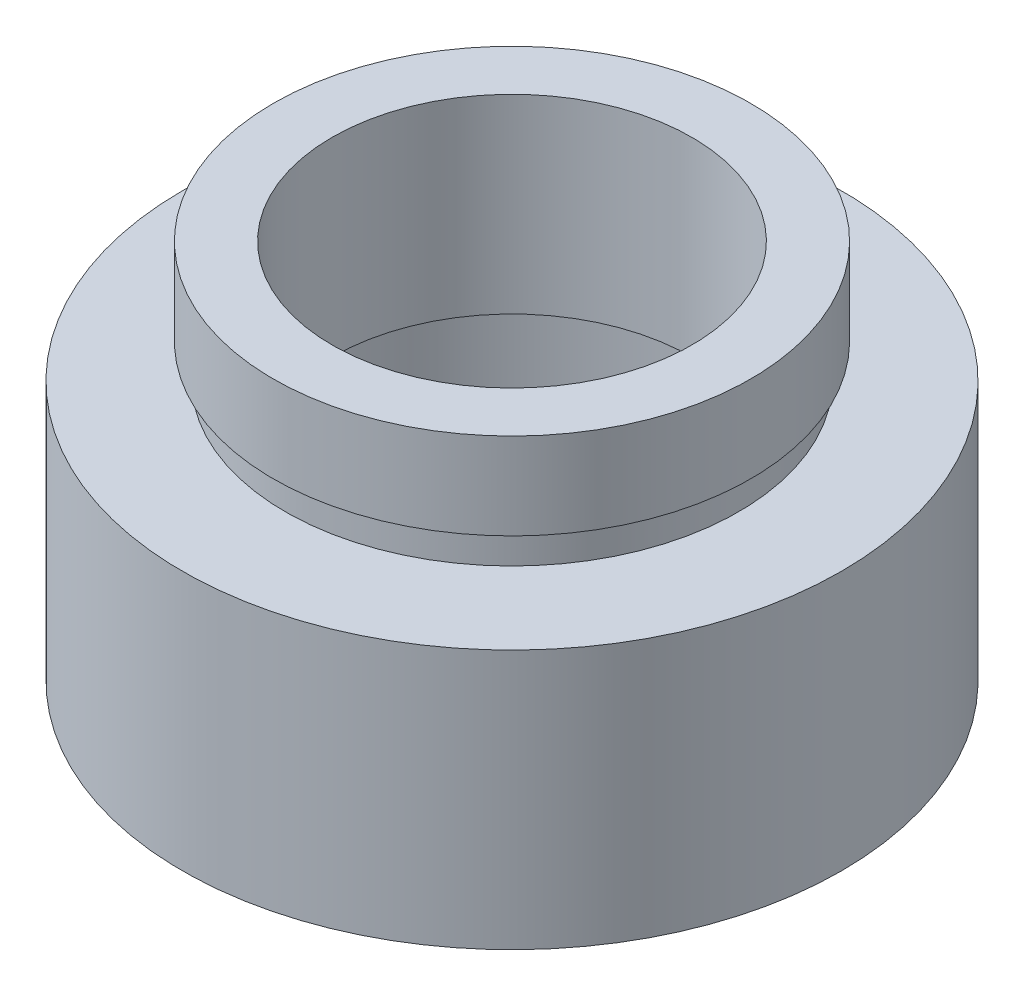
SolidWorks part; units mm, degrees
ref_plane "前视基准面" through (0, 0, 0) normal (0, 0, 1) x (1, 0, 0)
ref_plane "上视基准面" through (0, 0, 0) normal (0, 1, 0) x (1, 0, 0)
ref_plane "右视基准面" through (0, 0, 0) normal (1, 0, 0) x (0, 0, -1)
sketch "草图1" plane through (0, 0, 0) normal (0, 0, 1) x (1, 0, 0)
  line L0 (0, 16.886) -> (0, -24.4878) construction
  line L1 (7, 0) -> (7, 4.5)
  line L2 (5.2, 5.5) -> (7.6, 5.5)
  line L3 (5.2, 5.5) -> (5.2, 11)
  line L4 (5.2, 11) -> (6.9, 11)
  line L5 (6.9, 11) -> (6.9, 8.5)
  line L6 (6.9, 8.5) -> (6.55, 8.5)
  line L7 (6.55, 8.5) -> (6.55, 7.5)
  line L8 (6.55, 7.5) -> (9.525, 7.5)
  line L9 (9.525, 7.5) -> (9.525, 0)
  line L10 (9.525, 0) -> (7, 0)
  line L11 (7, 4.5) -> (7.6, 4.5)
  line L12 (7.6, 4.5) -> (7.6, 5.5)
  line L13 (0, 0) -> (3.4668, 0) construction
  point P4 (8.2625, 0)
  dimension "D1" = 5.2
  dimension "D2" = 6.9
  dimension "D3" = 6.55
  dimension "D4" = 7
  dimension "D5" = 7.6
  dimension "D6" = 9.525
  dimension "D7" = 11
  dimension "D8" = 7.5
  dimension "D9" = 1
  dimension "D10" = 4.5
  dimension "D11" = 1
revolve "旋转1" add sketch "草图1" angle 360 about L0
cosmetic thread "装饰螺纹线1" parameters "D2"=13.59
cosmetic thread "装饰螺纹线2" parameters "D2"=11
cosmetic thread "装饰螺纹线3" parameters "D2"=15
